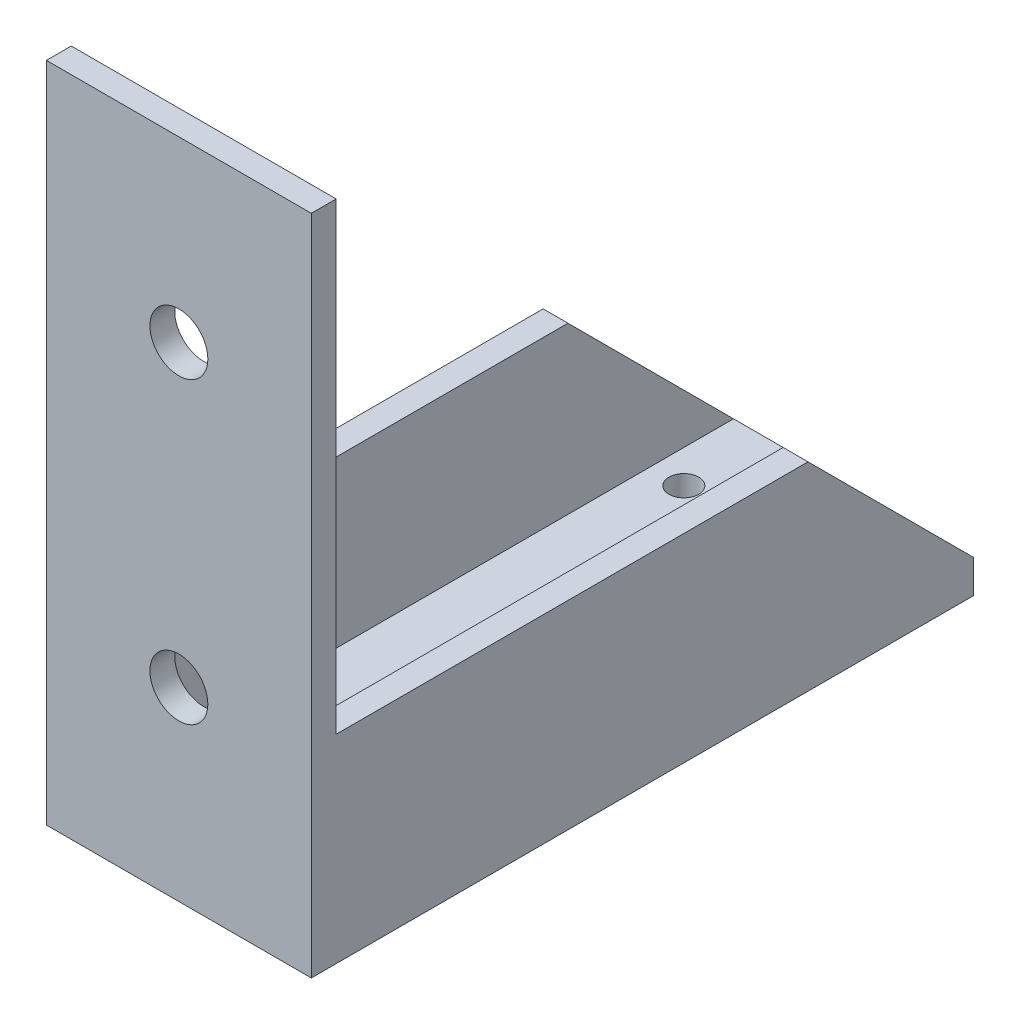
SolidWorks part; units mm, degrees
ref_plane "Front Plane" through (0, 0, 0) normal (0, 0, 1) x (1, 0, 0)
ref_plane "Top Plane" through (0, 0, 0) normal (0, 1, 0) x (1, 0, 0)
ref_plane "Right Plane" through (0, 0, 0) normal (1, 0, 0) x (0, 0, -1)
sketch "Sketch1" plane through (0, 0, 0) normal (0, 1, 0) x (1, 0, 0)
  line L1 (0, 0) -> (16, 0)
  line L2 (0, 0) -> (0, 40)
  line L3 (0, 40) -> (16, 40)
  line L4 (16, 0) -> (16, 40)
  circle A0 centre (8, 35) radius 2.3
  circle A1 centre (3.5, 35) radius 0.9
  circle A2 centre (12.5, 35) radius 0.9
  point P11 (0, 0)
  point P12 (0, 0)
  point P13 (0, 0)
  dimension "D1" = 4.6
  dimension "D6" = 1.8
  dimension "D7" = 1.8
  dimension "D2" = 16
  dimension "D3" = 9
  dimension "D4" = 4.5
  dimension "D5" = 5
  dimension "D8" = 8
  dimension "D9" = 40
extrude "Boss-Extrude1" add sketch "Sketch1" along normal blind 2
sketch "Sketch2" plane through (0, 0, 0) normal (-1, 0, 0) x (0, 0, 1)
  line L0 (-40, 2) -> (-30, 12)
  line L1 (-30, 12) -> (0, 12)
  line L2 (0, 12) -> (0, 2)
  line L3 (-40, 2) -> (0, 2) construction
  line L4 (0, 2) -> (-40, 2)
  dimension "D1" = 45
  dimension "D2" = 10
sketch "Sketch3" plane through (16, 0, -16) normal (-1, 0, 0) x (0, 0, 1)
  line L0 (-24, 2) -> (-14, 12)
  line L1 (-14, 12) -> (16, 12)
  line L2 (16, 12) -> (16, 2)
  line L4 (16, 2) -> (-24, 2)
  point P4 (0, 0)
  point P6 (0, 0)
  point P7 (-29.1795, 2)
  dimension "D1" = 45
  dimension "D2" = 10
extrude "Boss-Extrude2" add sketch "Sketch2" against normal blind 1.5 contours L1 L2 L4 L0
extrude "Boss-Extrude3" add sketch "Sketch3" along normal blind 1.5 contours L1 L2 L4 L0
sketch "Sketch4" plane through (0, 0, 0) normal (0, 0, 1) x (1, 0, 0)
  line L0 (16, 12) -> (16, 0) construction
  line L1 (0, 0) -> (16, 0)
  line L2 (0, 0) -> (0, 40)
  line L3 (0, 40) -> (16, 40)
  line L4 (16, 0) -> (16, 40)
  circle A0 centre (8, 11.1976) radius 1.75
  circle A1 centre (8, 29.2496) radius 1.75
  point P11 (0, 0)
  dimension "D3" = 3.5
  dimension "D1" = 40
  dimension "D2" = 8
extrude "Boss-Extrude4" add sketch "Sketch4" against normal blind 1.5
